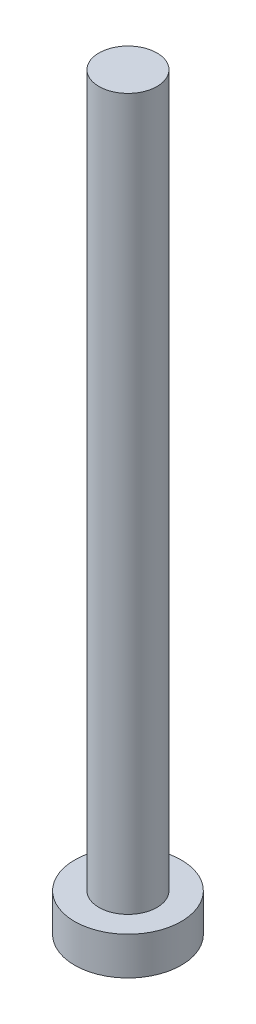
SolidWorks part; units mm, degrees
ref_plane "Front Plane" through (0, 0, 0) normal (0, 0, 1) x (1, 0, 0)
ref_plane "Top Plane" through (0, 0, 0) normal (0, 1, 0) x (1, 0, 0)
ref_plane "Right Plane" through (0, 0, 0) normal (1, 0, 0) x (0, 0, -1)
sketch "Sketch1" plane through (0, 0, 0) normal (0, 1, 0) x (1, 0, 0)
  circle A0 centre (0, 0) radius 2.25
  dimension "D1" = 4.5
extrude "Boss-Extrude1" add sketch "Sketch1" along normal blind 1.6
sketch "Sketch2" plane through (0, 1.6, 0) normal (0, 1, 0) x (1, 0, 0)
  circle A0 centre (0, 0) radius 1.225
  dimension "D1" = 2.45
extrude "Boss-Extrude2" add sketch "Sketch2" along normal blind 30
